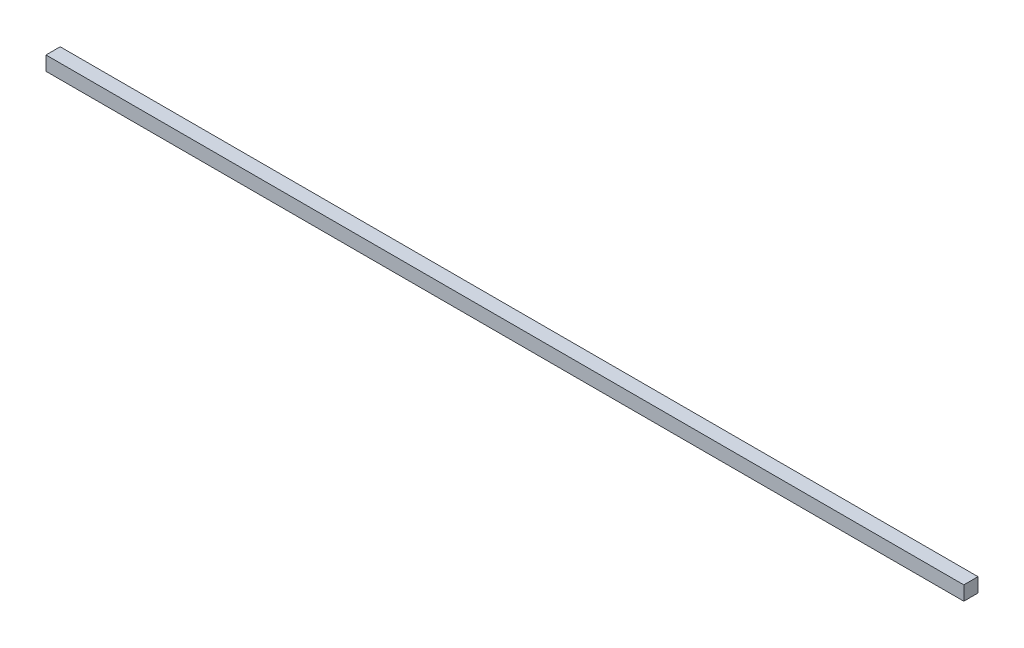
SolidWorks part; units mm, degrees
material "Plywood"
ref_plane "Front Plane" through (0, 0, 0) normal (0, 0, 1) x (1, 0, 0)
ref_plane "Top Plane" through (0, 0, 0) normal (0, 1, 0) x (1, 0, 0)
ref_plane "Right Plane" through (0, 0, 0) normal (1, 0, 0) x (0, 0, -1)
sketch "Sketch1" plane through (0, 0, 0) normal (1, 0, 0) x (0, 0, -1)
  line L1 (0, 0) -> (4.7625, 0)
  line L2 (0, 0) -> (0, 4.7625)
  line L3 (0, 4.7625) -> (4.7625, 4.7625)
  line L4 (4.7625, 0) -> (4.7625, 4.7625)
  dimension "D1" = 4.7625
extrude "Boss-Extrude1" add sketch "Sketch1" against normal blind 307.975 contours L1 L4 L3 L2
move or copy body "Body-Move/Copy1" [suppressed] bodies to move or copy 101 parameters "D1"=0, "D2"=0, "D3"=0
move or copy body "Body-Move/Copy2" [suppressed] bodies to move or copy 102 parameters "D1"=0, "D2"=0, "D3"=0
move or copy body "Body-Move/Copy3" [suppressed] bodies to move or copy 103 parameters "D1"=0, "D2"=0, "D3"=0
move or copy body "Body-Move/Copy4" [suppressed] bodies to move or copy 104 parameters "D1"=0, "D2"=0, "D3"=0
move or copy body "Body-Move/Copy5" [suppressed] bodies to move or copy 105 parameters "D1"=0, "D2"=0, "D3"=0
move or copy body "Body-Move/Copy6" [suppressed] bodies to move or copy 106 parameters "D1"=0, "D2"=0, "D3"=0
move or copy body "Body-Move/Copy7" [suppressed] bodies to move or copy 107 parameters "D1"=0, "D2"=0, "D3"=0
move or copy body "Body-Move/Copy8" [suppressed] bodies to move or copy 108 parameters "D1"=0, "D2"=0, "D3"=0
move or copy body "Body-Move/Copy9" [suppressed] bodies to move or copy 109 parameters "D1"=0, "D2"=0, "D3"=0
move or copy body "Body-Move/Copy10" [suppressed] bodies to move or copy 110 parameters "D1"=0, "D2"=0, "D3"=0
